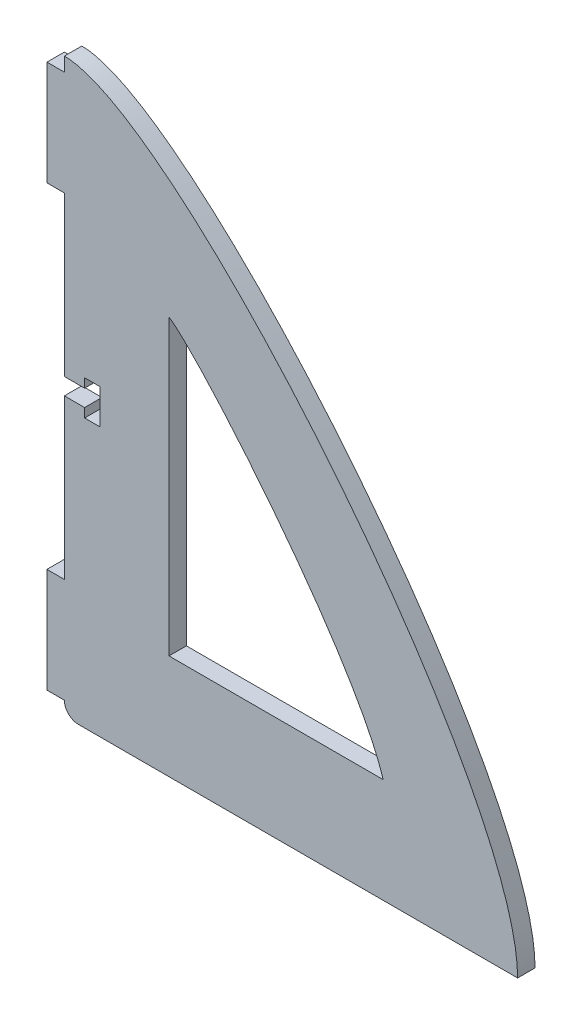
SolidWorks part; units mm, degrees
ref_plane "Front Plane" through (0, 0, 0) normal (0, 0, 1) x (1, 0, 0)
ref_plane "Top Plane" through (0, 0, 0) normal (0, 1, 0) x (1, 0, 0)
ref_plane "Right Plane" through (0, 0, 0) normal (1, 0, 0) x (0, 0, -1)
sketch "Sketch1" plane through (0, 0, 0) normal (0, 0, 1) x (1, 0, 0)
  line L0 (0, 82.55) -> (0, 53.594)
  line L1 (2.54, 0) -> (82.55, 0)
  line L2 (0, 101.6) -> (0, 104.14)
  line L3 (0, 101.6) -> (24.3064, 101.6) construction
  line L4 (7.5545, 104.14) -> (6.6359, 104.14) construction
  line L5 (82.55, -16.8979) -> (82.55, 16.8979) construction
  line L6 (0, 101.6) -> (-3.175, 101.6)
  line L7 (-3.175, 101.6) -> (-3.175, 82.55)
  line L8 (-3.175, 82.55) -> (0, 82.55)
  line L9 (0, 2.54) -> (-3.175, 2.54)
  line L10 (-3.175, 2.54) -> (-3.175, 21.59)
  line L11 (19.05, 72.5277) -> (19.05, 19.05)
  line L12 (19.05, 19.05) -> (58.0733, 19.05)
  line L13 (-3.175, 21.59) -> (0, 21.59)
  line L14 (0, 2.54) -> (0, 21.59) construction
  line L15 (0, 82.55) -> (0, 101.6) construction
  line L16 (0, 53.594) -> (3.683, 53.594)
  line L17 (3.683, 53.594) -> (3.683, 55.245)
  line L18 (3.683, 55.245) -> (6.477, 55.245)
  line L19 (6.477, 55.245) -> (6.477, 48.895)
  line L20 (6.477, 48.895) -> (3.683, 48.895)
  line L21 (3.683, 48.895) -> (3.683, 50.546)
  line L22 (3.683, 50.546) -> (0, 50.546)
  line L23 (0, 50.546) -> (0, 21.59)
  arc A0 (0, 2.54) -> (2.54, 0) centre (2.54, 2.54) ccw
  spline S0 degree 3 poles (0, 104.14) (20.8157, 104.14) (82.55, 29.5601) (82.55, 0) knots 0 0 0 0 1 1 1 1
  spline S1 degree 3 poles (19.05, 72.5277) (24.9796, 68.6376) (52.982, 35.4593) (58.0733, 19.05) knots 0 0 0 0 1 1 1 1
  point P8 (0, 0)
  dimension "D5" = 2.54
  dimension "D1" = 90
  dimension "D2" = 82.55
  dimension "D3" = 101.6
  dimension "D4" = 19.05
  dimension "D6" = 19.05
  dimension "D7" = 3.175
  dimension "D8" = 19.05
  dimension "D9" = 19.05
  dimension "D10" = 3.175
  dimension "D11" = 2.54
  dimension "D12" = 2.794
  dimension "D13" = 6.35
  dimension "D14" = 3.048
  dimension "D15" = 6.477
  dimension "D16" = 28.956
extrude "Boss-Extrude1" add sketch "Sketch1" along normal blind 3.175
